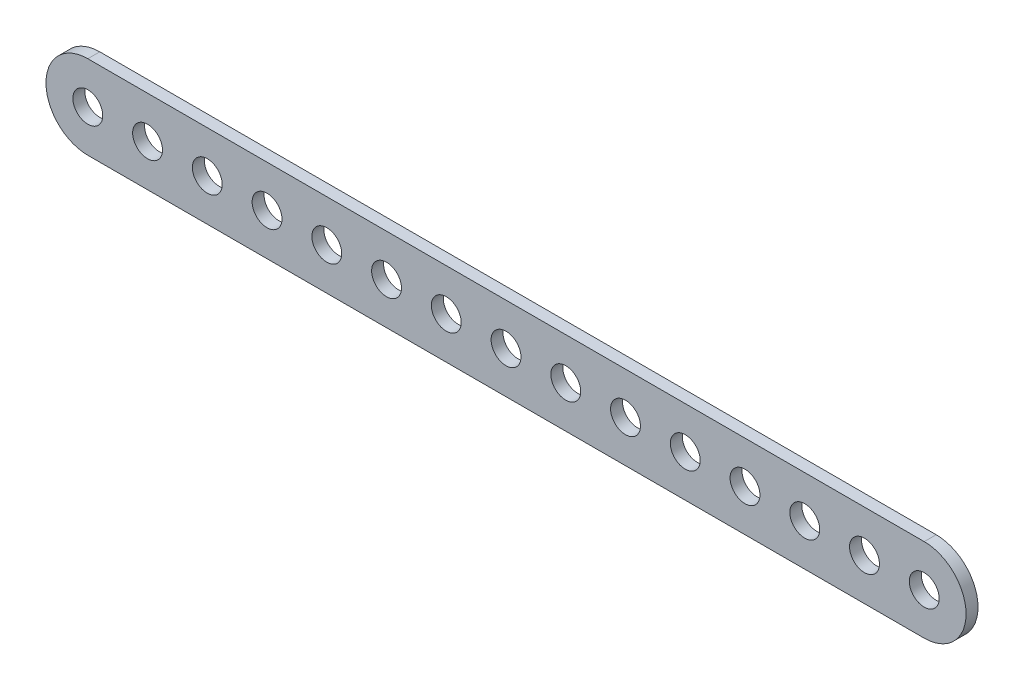
SolidWorks part; units mm, degrees
ref_plane "Front Plane" through (0, 0, 0) normal (0, 0, 1) x (1, 0, 0)
ref_plane "Top Plane" through (0, 0, 0) normal (0, 1, 0) x (1, 0, 0)
ref_plane "Right Plane" through (0, 0, 0) normal (1, 0, 0) x (0, 0, -1)
sketch "Sketch1" plane through (0, 0, 0) normal (0, 0, 1) x (1, 0, 0)
  line L0 (0, 0) -> (12.5, 0) construction
  line L1 (0, 35) -> (700, 35)
  line L2 (0, -35) -> (700, -35)
  line L3 (500, 0) -> (687.5, 0) construction
  line L4 (687.5, 0) -> (0, 0) construction
  arc A0 (0, 35) -> (0, -35) centre (0, 0) ccw
  arc A1 (700, -35) -> (700, 35) centre (700, 0) ccw
  circle A3 centre (0, 0) radius 1.7247
  circle A4 centre (0, 0) radius 12.5
  circle A5 centre (50, 0) radius 12.5
  circle A6 centre (100, 0) radius 12.5
  circle A7 centre (150, 0) radius 12.5
  circle A8 centre (200, 0) radius 12.5
  circle A9 centre (250, 0) radius 12.5
  circle A10 centre (300, 0) radius 12.5
  circle A11 centre (350, 0) radius 12.5
  circle A12 centre (400, 0) radius 12.5
  circle A13 centre (450, 0) radius 12.5
  circle A14 centre (500, 0) radius 12.5
  circle A15 centre (550, 0) radius 12.5
  circle A16 centre (600, 0) radius 12.5
  circle A17 centre (650, 0) radius 12.5
  circle A18 centre (700, 0) radius 12.5
  point P3 (500, 0)
  dimension "D2" = 35
  dimension "D3" = 25
  dimension "D4" = 15
  dimension "D1" = 700
extrude "Boss-Extrude1" add sketch "Sketch1" along normal blind 10
